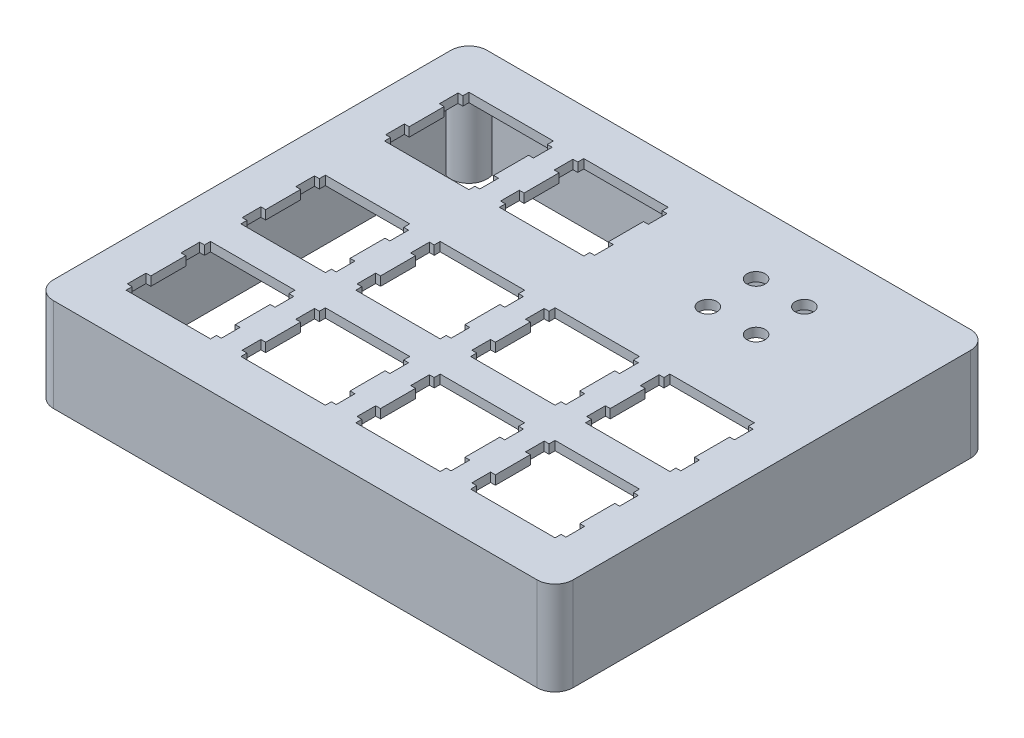
SolidWorks part; units mm, degrees
material "ABS"
ref_plane "Front" through (0, 0, 0) normal (0, 0, 1) x (1, 0, 0)
ref_plane "Top" through (0, 0, 0) normal (0, 1, 0) x (1, 0, 0)
ref_plane "Right" through (0, 0, 0) normal (1, 0, 0) x (0, 0, -1)
sketch "Model" plane through (0, 0, -8.6083) normal (0, 1, 0) x (1, 0, 0)
  line L0 (59.625, 24.9677) -> (64.675, 24.9677) construction
  line L1 (62.15, 24.9677) -> (62.15, 48.7802) construction
  line L3 (58.15, 52.7802) -> (66.15, 52.7802) construction
  line L4 (58.15, 52.7802) -> (58.15, 44.7802) construction
  line L5 (58.15, 44.7802) -> (66.15, 44.7802) construction
  line L6 (66.15, 52.7802) -> (66.15, 44.7802) construction
  line L7 (58.15, 52.7802) -> (66.15, 44.7802) construction
  line L8 (58.15, 44.7802) -> (66.15, 52.7802) construction
  circle A0 centre (58.15, 52.7802) radius 1.5
  circle A1 centre (66.15, 52.7802) radius 1.5
  circle A2 centre (66.15, 44.7802) radius 1.5
  circle A3 centre (58.15, 44.7802) radius 1.5
  point P5 (40.575, 48.7802)
  line B0 (86.201, -8.6083) -> (0, -8.6083)
  line B1 (0, -8.6083) -> (0, 63.3047)
  line B2 (0, 63.3047) -> (86.201, 63.3047)
  line B3 (86.201, 63.3047) -> (86.201, -8.6083)
  line B4 (64.675, 12.9177) -> (64.675, 11.9177)
  line B5 (64.675, 11.9177) -> (63.875, 11.9177)
  line B6 (63.875, 11.9177) -> (63.875, 8.8177)
  line B7 (63.875, 8.8177) -> (64.675, 8.8177)
  line B8 (64.675, 8.8177) -> (64.675, 3.0177)
  line B9 (64.675, 3.0177) -> (63.875, 3.0177)
  line B10 (63.875, 3.0177) -> (63.875, -0.0823)
  line B11 (63.875, -0.0823) -> (64.675, -0.0823)
  line B12 (64.675, -0.0823) -> (64.675, -1.0823)
  line B13 (64.675, -1.0823) -> (78.675, -1.0823)
  line B14 (78.675, -1.0823) -> (78.675, -0.0823)
  line B15 (78.675, -0.0823) -> (79.475, -0.0823)
  line B16 (79.475, -0.0823) -> (79.475, 3.0177)
  line B17 (79.475, 3.0177) -> (78.675, 3.0177)
  line B18 (78.675, 3.0177) -> (78.675, 8.8177)
  line B19 (78.675, 8.8177) -> (79.475, 8.8177)
  line B20 (79.475, 8.8177) -> (79.475, 11.9177)
  line B21 (79.475, 11.9177) -> (78.675, 11.9177)
  line B22 (78.675, 11.9177) -> (78.675, 12.9177)
  line B23 (78.675, 12.9177) -> (64.675, 12.9177)
  line B24 (45.625, 12.9177) -> (45.625, 11.9177)
  line B25 (45.625, 11.9177) -> (44.825, 11.9177)
  line B26 (44.825, 11.9177) -> (44.825, 8.8177)
  line B27 (44.825, 8.8177) -> (45.625, 8.8177)
  line B28 (45.625, 8.8177) -> (45.625, 3.0177)
  line B29 (45.625, 3.0177) -> (44.825, 3.0177)
  line B30 (44.825, 3.0177) -> (44.825, -0.0823)
  line B31 (44.825, -0.0823) -> (45.625, -0.0823)
  line B32 (45.625, -0.0823) -> (45.625, -1.0823)
  line B33 (45.625, -1.0823) -> (59.625, -1.0823)
  line B34 (59.625, -1.0823) -> (59.625, -0.0823)
  line B35 (59.625, -0.0823) -> (60.425, -0.0823)
  line B36 (60.425, -0.0823) -> (60.425, 3.0177)
  line B37 (60.425, 3.0177) -> (59.625, 3.0177)
  line B38 (59.625, 3.0177) -> (59.625, 8.8177)
  line B39 (59.625, 8.8177) -> (60.425, 8.8177)
  line B40 (60.425, 8.8177) -> (60.425, 11.9177)
  line B41 (60.425, 11.9177) -> (59.625, 11.9177)
  line B42 (59.625, 11.9177) -> (59.625, 12.9177)
  line B43 (59.625, 12.9177) -> (45.625, 12.9177)
  line B44 (26.575, 12.9177) -> (26.575, 11.9177)
  line B45 (26.575, 11.9177) -> (25.775, 11.9177)
  line B46 (25.775, 11.9177) -> (25.775, 8.8177)
  line B47 (25.775, 8.8177) -> (26.575, 8.8177)
  line B48 (26.575, 8.8177) -> (26.575, 3.0177)
  line B49 (26.575, 3.0177) -> (25.775, 3.0177)
  line B50 (25.775, 3.0177) -> (25.775, -0.0823)
  line B51 (25.775, -0.0823) -> (26.575, -0.0823)
  line B52 (26.575, -0.0823) -> (26.575, -1.0823)
  line B53 (26.575, -1.0823) -> (40.575, -1.0823)
  line B54 (40.575, -1.0823) -> (40.575, -0.0823)
  line B55 (40.575, -0.0823) -> (41.375, -0.0823)
  line B56 (41.375, -0.0823) -> (41.375, 3.0177)
  line B57 (41.375, 3.0177) -> (40.575, 3.0177)
  line B58 (40.575, 3.0177) -> (40.575, 8.8177)
  line B59 (40.575, 8.8177) -> (41.375, 8.8177)
  line B60 (41.375, 8.8177) -> (41.375, 11.9177)
  line B61 (41.375, 11.9177) -> (40.575, 11.9177)
  line B62 (40.575, 11.9177) -> (40.575, 12.9177)
  line B63 (40.575, 12.9177) -> (26.575, 12.9177)
  line B64 (7.524, 12.9177) -> (7.524, 11.9177)
  line B65 (7.524, 11.9177) -> (6.724, 11.9177)
  line B66 (6.724, 11.9177) -> (6.724, 8.8177)
  line B67 (6.724, 8.8177) -> (7.524, 8.8177)
  line B68 (7.524, 8.8177) -> (7.524, 3.0177)
  line B69 (7.524, 3.0177) -> (6.724, 3.0177)
  line B70 (6.724, 3.0177) -> (6.724, -0.0823)
  line B71 (6.724, -0.0823) -> (7.524, -0.0823)
  line B72 (7.524, -0.0823) -> (7.524, -1.0823)
  line B73 (7.524, -1.0823) -> (21.525, -1.0823)
  line B74 (21.525, -1.0823) -> (21.525, -0.0823)
  line B75 (21.525, -0.0823) -> (22.325, -0.0823)
  line B76 (22.325, -0.0823) -> (22.325, 3.0177)
  line B77 (22.325, 3.0177) -> (21.525, 3.0177)
  line B78 (21.525, 3.0177) -> (21.525, 8.8177)
  line B79 (21.525, 8.8177) -> (22.325, 8.8177)
  line B80 (22.325, 8.8177) -> (22.325, 11.9177)
  line B81 (22.325, 11.9177) -> (21.525, 11.9177)
  line B82 (21.525, 11.9177) -> (21.525, 12.9177)
  line B83 (21.525, 12.9177) -> (7.524, 12.9177)
  line B84 (64.675, 31.9677) -> (64.675, 30.9677)
  line B85 (64.675, 30.9677) -> (63.875, 30.9677)
  line B86 (63.875, 30.9677) -> (63.875, 27.8677)
  line B87 (63.875, 27.8677) -> (64.675, 27.8677)
  line B88 (64.675, 27.8677) -> (64.675, 22.0677)
  line B89 (64.675, 22.0677) -> (63.875, 22.0677)
  line B90 (63.875, 22.0677) -> (63.875, 18.9677)
  line B91 (63.875, 18.9677) -> (64.675, 18.9677)
  line B92 (64.675, 18.9677) -> (64.675, 17.9677)
  line B93 (64.675, 17.9677) -> (78.675, 17.9677)
  line B94 (78.675, 17.9677) -> (78.675, 18.9677)
  line B95 (78.675, 18.9677) -> (79.475, 18.9677)
  line B96 (79.475, 18.9677) -> (79.475, 22.0677)
  line B97 (79.475, 22.0677) -> (78.675, 22.0677)
  line B98 (78.675, 22.0677) -> (78.675, 27.8677)
  line B99 (78.675, 27.8677) -> (79.475, 27.8677)
  line B100 (79.475, 27.8677) -> (79.475, 30.9677)
  line B101 (79.475, 30.9677) -> (78.675, 30.9677)
  line B102 (78.675, 30.9677) -> (78.675, 31.9677)
  line B103 (78.675, 31.9677) -> (64.675, 31.9677)
  line B104 (45.625, 31.9677) -> (45.625, 30.9677)
  line B105 (45.625, 30.9677) -> (44.825, 30.9677)
  line B106 (44.825, 30.9677) -> (44.825, 27.8677)
  line B107 (44.825, 27.8677) -> (45.625, 27.8677)
  line B108 (45.625, 27.8677) -> (45.625, 22.0677)
  line B109 (45.625, 22.0677) -> (44.825, 22.0677)
  line B110 (44.825, 22.0677) -> (44.825, 18.9677)
  line B111 (44.825, 18.9677) -> (45.625, 18.9677)
  line B112 (45.625, 18.9677) -> (45.625, 17.9677)
  line B113 (45.625, 17.9677) -> (59.625, 17.9677)
  line B114 (59.625, 17.9677) -> (59.625, 18.9677)
  line B115 (59.625, 18.9677) -> (60.425, 18.9677)
  line B116 (60.425, 18.9677) -> (60.425, 22.0677)
  line B117 (60.425, 22.0677) -> (59.625, 22.0677)
  line B118 (59.625, 22.0677) -> (59.625, 27.8677)
  line B119 (59.625, 27.8677) -> (60.425, 27.8677)
  line B120 (60.425, 27.8677) -> (60.425, 30.9677)
  line B121 (60.425, 30.9677) -> (59.625, 30.9677)
  line B122 (59.625, 30.9677) -> (59.625, 31.9677)
  line B123 (59.625, 31.9677) -> (45.625, 31.9677)
  line B124 (26.575, 31.9677) -> (26.575, 30.9677)
  line B125 (26.575, 30.9677) -> (25.775, 30.9677)
  line B126 (25.775, 30.9677) -> (25.775, 27.8677)
  line B127 (25.775, 27.8677) -> (26.575, 27.8677)
  line B128 (26.575, 27.8677) -> (26.575, 22.0677)
  line B129 (26.575, 22.0677) -> (25.775, 22.0677)
  line B130 (25.775, 22.0677) -> (25.775, 18.9677)
  line B131 (25.775, 18.9677) -> (26.575, 18.9677)
  line B132 (26.575, 18.9677) -> (26.575, 17.9677)
  line B133 (26.575, 17.9677) -> (40.575, 17.9677)
  line B134 (40.575, 17.9677) -> (40.575, 18.9677)
  line B135 (40.575, 18.9677) -> (41.375, 18.9677)
  line B136 (41.375, 18.9677) -> (41.375, 22.0677)
  line B137 (41.375, 22.0677) -> (40.575, 22.0677)
  line B138 (40.575, 22.0677) -> (40.575, 27.8677)
  line B139 (40.575, 27.8677) -> (41.375, 27.8677)
  line B140 (41.375, 27.8677) -> (41.375, 30.9677)
  line B141 (41.375, 30.9677) -> (40.575, 30.9677)
  line B142 (40.575, 30.9677) -> (40.575, 31.9677)
  line B143 (40.575, 31.9677) -> (26.575, 31.9677)
  line B144 (7.524, 31.9677) -> (7.524, 30.9677)
  line B145 (7.524, 30.9677) -> (6.724, 30.9677)
  line B146 (6.724, 30.9677) -> (6.724, 27.8677)
  line B147 (6.724, 27.8677) -> (7.524, 27.8677)
  line B148 (7.524, 27.8677) -> (7.524, 22.0677)
  line B149 (7.524, 22.0677) -> (6.724, 22.0677)
  line B150 (6.724, 22.0677) -> (6.724, 18.9677)
  line B151 (6.724, 18.9677) -> (7.524, 18.9677)
  line B152 (7.524, 18.9677) -> (7.524, 17.9677)
  line B153 (7.524, 17.9677) -> (21.525, 17.9677)
  line B154 (21.525, 17.9677) -> (21.525, 18.9677)
  line B155 (21.525, 18.9677) -> (22.325, 18.9677)
  line B156 (22.325, 18.9677) -> (22.325, 22.0677)
  line B157 (22.325, 22.0677) -> (21.525, 22.0677)
  line B158 (21.525, 22.0677) -> (21.525, 27.8677)
  line B159 (21.525, 27.8677) -> (22.325, 27.8677)
  line B160 (22.325, 27.8677) -> (22.325, 30.9677)
  line B161 (22.325, 30.9677) -> (21.525, 30.9677)
  line B162 (21.525, 30.9677) -> (21.525, 31.9677)
  line B163 (21.525, 31.9677) -> (7.524, 31.9677)
  line B164 (26.575, 55.7807) -> (26.575, 54.7807)
  line B165 (26.575, 54.7807) -> (25.775, 54.7807)
  line B166 (25.775, 54.7807) -> (25.775, 51.6797)
  line B167 (25.775, 51.6797) -> (26.575, 51.6797)
  line B168 (26.575, 51.6797) -> (26.575, 45.8807)
  line B169 (26.575, 45.8807) -> (25.775, 45.8807)
  line B170 (25.775, 45.8807) -> (25.775, 42.7797)
  line B171 (25.775, 42.7797) -> (26.575, 42.7797)
  line B172 (26.575, 42.7797) -> (26.575, 41.7797)
  line B173 (26.575, 41.7797) -> (40.575, 41.7797)
  line B174 (40.575, 41.7797) -> (40.575, 42.7797)
  line B175 (40.575, 42.7797) -> (41.375, 42.7797)
  line B176 (41.375, 42.7797) -> (41.375, 45.8807)
  line B177 (41.375, 45.8807) -> (40.575, 45.8807)
  line B178 (40.575, 45.8807) -> (40.575, 51.6797)
  line B179 (40.575, 51.6797) -> (41.375, 51.6797)
  line B180 (41.375, 51.6797) -> (41.375, 54.7807)
  line B181 (41.375, 54.7807) -> (40.575, 54.7807)
  line B182 (40.575, 54.7807) -> (40.575, 55.7807)
  line B183 (40.575, 55.7807) -> (26.575, 55.7807)
  line B184 (7.524, 55.7807) -> (7.524, 54.7807)
  line B185 (7.524, 54.7807) -> (6.724, 54.7807)
  line B186 (6.724, 54.7807) -> (6.724, 51.6797)
  line B187 (6.724, 51.6797) -> (7.524, 51.6797)
  line B188 (7.524, 51.6797) -> (7.524, 45.8807)
  line B189 (7.524, 45.8807) -> (6.724, 45.8807)
  line B190 (6.724, 45.8807) -> (6.724, 42.7797)
  line B191 (6.724, 42.7797) -> (7.524, 42.7797)
  line B192 (7.524, 42.7797) -> (7.524, 41.7797)
  line B193 (7.524, 41.7797) -> (21.525, 41.7797)
  line B194 (21.525, 41.7797) -> (21.525, 42.7797)
  line B195 (21.525, 42.7797) -> (22.325, 42.7797)
  line B196 (22.325, 42.7797) -> (22.325, 45.8807)
  line B197 (22.325, 45.8807) -> (21.525, 45.8807)
  line B198 (21.525, 45.8807) -> (21.525, 51.6797)
  line B199 (21.525, 51.6797) -> (22.325, 51.6797)
  line B200 (22.325, 51.6797) -> (22.325, 54.7807)
  line B201 (22.325, 54.7807) -> (21.525, 54.7807)
  line B202 (21.525, 54.7807) -> (21.525, 55.7807)
  line B203 (21.525, 55.7807) -> (7.524, 55.7807)
  dimension "D1" = 3
  dimension "D2" = 8
sketch_block_instance "Block1-1"
sketch_block "Block1"
extrude "Boss-Extrude1" add sketch "Model" against normal blind 1.5
sketch "Sketch1" plane through (0, -1.5, 0) normal (0, -1, 0) x (-1, 0, 0)
  line L1 (0, 0) -> (-86.201, 0)
  line L2 (0, 0) -> (0, 71.913)
  line L3 (0, 71.913) -> (-86.201, 71.913)
  line L4 (-86.201, 0) -> (-86.201, 71.913)
extrude "Extrude-Thin1" add sketch "Sketch1" along normal blind 14 thin
fillet "Fillet1" radius 3 4 edges at (0, -7.75, 0) (86.201, -7.75, -71.913) (0, -7.75, -71.913) (86.201, -7.75, 0)
sketch "Sketch2" plane through (0, -15.5, 0) normal (0, -1, 0) x (1, 0, 0)
  circle A0 centre (3, -3) radius 3
  arc A1 (3, 0) -> (0, -3) centre (3, -3) ccw construction
  circle A2 centre (83.201, -3) radius 3
  circle A3 centre (3, -68.913) radius 3
  circle A4 centre (83.201, -68.913) radius 3
  arc A5 (83.201, -71.913) -> (86.201, -68.913) centre (83.201, -68.913) ccw construction
  arc A6 (0, -68.913) -> (3, -71.913) centre (3, -68.913) ccw construction
  arc A7 (86.201, -3) -> (83.201, 0) centre (83.201, -3) ccw construction
extrude "Boss-Extrude2" add sketch "Sketch2" against normal up to surface (14 mm away) contours A2
hole_wizard "Tap Drill for #2-56 Tap1" positions "Sketch3" profile "Sketch5" hole size "#2-56" standard "ANSI Inch"
sketch "Sketch3" plane through (0, -15.5, 0) normal (0, -1, 0) x (-1, 0, 0)
  point P0 (-3, 3)
  point P3 (-83.201, 3)
  point P6 (-83.201, 68.913)
  point P9 (-3, 68.913)
sketch "Sketch5" plane through (3, -15.5, -3) normal (1, 0, 0) x (0, 0, -1)
  line L0 (0, 0) -> (0, 13.2342)
  line L1 (0, 13.2342) -> (0.889, 12.7)
  line L2 (0.889, 12.7) -> (0.889, 0)
  line L5 (0.889, 0) -> (0, 0)
  line L10 (0, 13.2342) -> (-0.889, 12.7) construction
  line L11 (0, -6.35) -> (0, 107.95) construction
  dimension "Hole Dia." = 1.778
  dimension "Hole Depth" = 12.7
  dimension "Drill Angle" = 118
sketch "Sketch6" plane through (0, 0, -71.913) normal (0, 0, -1) x (-1, 0, 0)
  line L0 (-3, -15.5) -> (-83.201, -15.5) construction
  line L2 (-47.1005, -22) -> (-39.1005, -22)
  line L3 (-47.1005, -22) -> (-47.1005, -9)
  line L4 (-47.1005, -9) -> (-39.1005, -9)
  line L5 (-39.1005, -22) -> (-39.1005, -9)
  line L6 (-47.1005, -22) -> (-39.1005, -9) construction
  line L7 (-47.1005, -9) -> (-39.1005, -22) construction
  point P0 (-43.1005, -15.5)
  point P1 (-43.1005, -15.5)
  dimension "D1" = 6.5
  dimension "D2" = 8
extrude "Cut-Extrude1" cut sketch "Sketch6" against normal up to surface (2 mm away) up to face at (43.1005, -8.5, -69.913)
